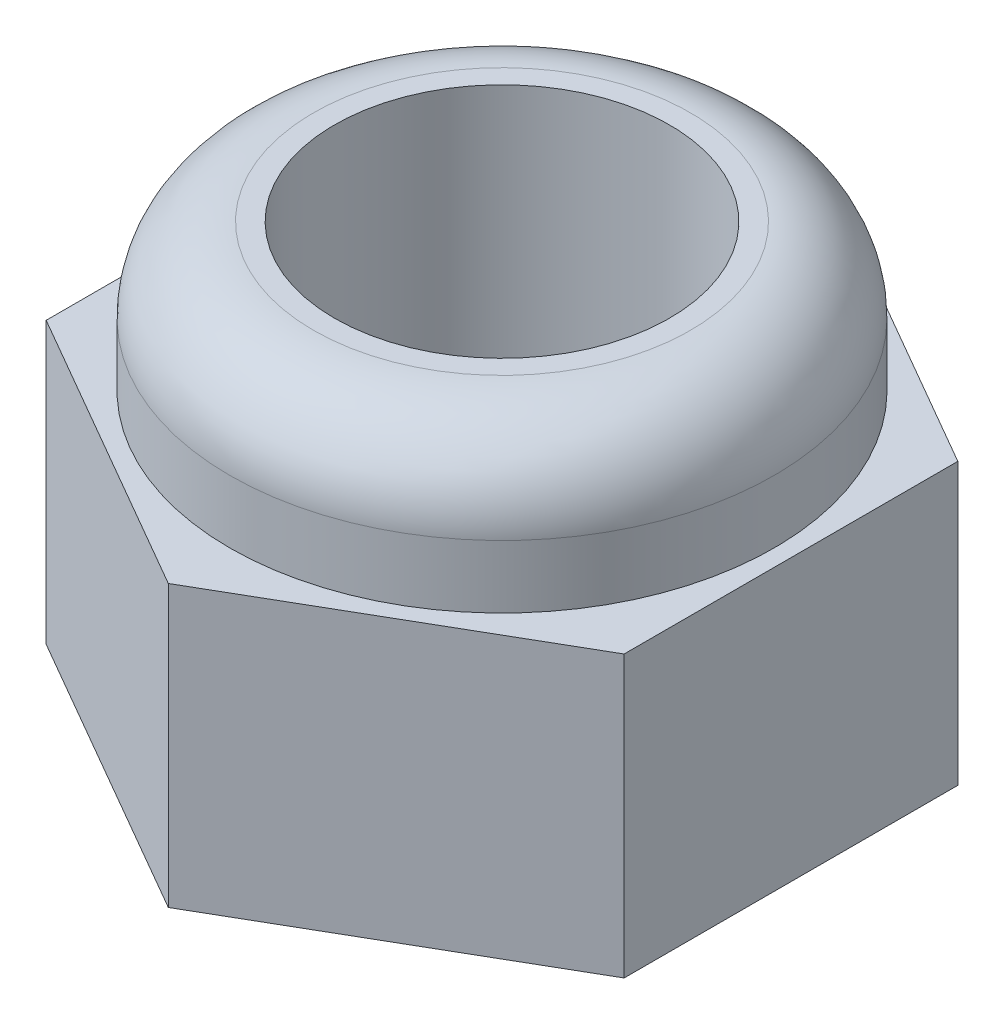
SolidWorks part; units mm, degrees
ref_plane "Front Plane" through (0, 0, 0) normal (0, 0, 1) x (1, 0, 0)
ref_plane "Top Plane" through (0, 0, 0) normal (0, 1, 0) x (1, 0, 0)
ref_plane "Right Plane" through (0, 0, 0) normal (1, 0, 0) x (0, 0, -1)
sketch "Sketch1" plane through (0, 0, 0) normal (0, 1, 0) x (1, 0, 0)
  line L1 (0, 3.9837) -> (-3.45, 1.9919)
  line L2 (-3.45, 1.9919) -> (-3.45, -1.9919)
  line L3 (-3.45, -1.9919) -> (0, -3.9837)
  line L4 (0, -3.9837) -> (3.45, -1.9919)
  line L5 (3.45, -1.9919) -> (3.45, 1.9919)
  line L6 (3.45, 1.9919) -> (0, 3.9837)
  circle A0 centre (0, 0) radius 3.45 construction
  circle A1 centre (0, 0) radius 2
  dimension "D1" = 6.9
  dimension "D2" = 4
extrude "Boss-Extrude1" add sketch "Sketch1" along normal blind 3.35
sketch "Sketch2" plane through (0, 3.35, 0) normal (0, 1, 0) x (1, 0, 0)
  circle A0 centre (0, 0) radius 2
  circle A1 centre (0, 0) radius 3.25
  dimension "D1" = 6.5
extrude "Boss-Extrude2" add sketch "Sketch2" along normal blind 1.75
fillet "Fillet1" radius 1 1 edges at (0, 5.1, 3.25)
